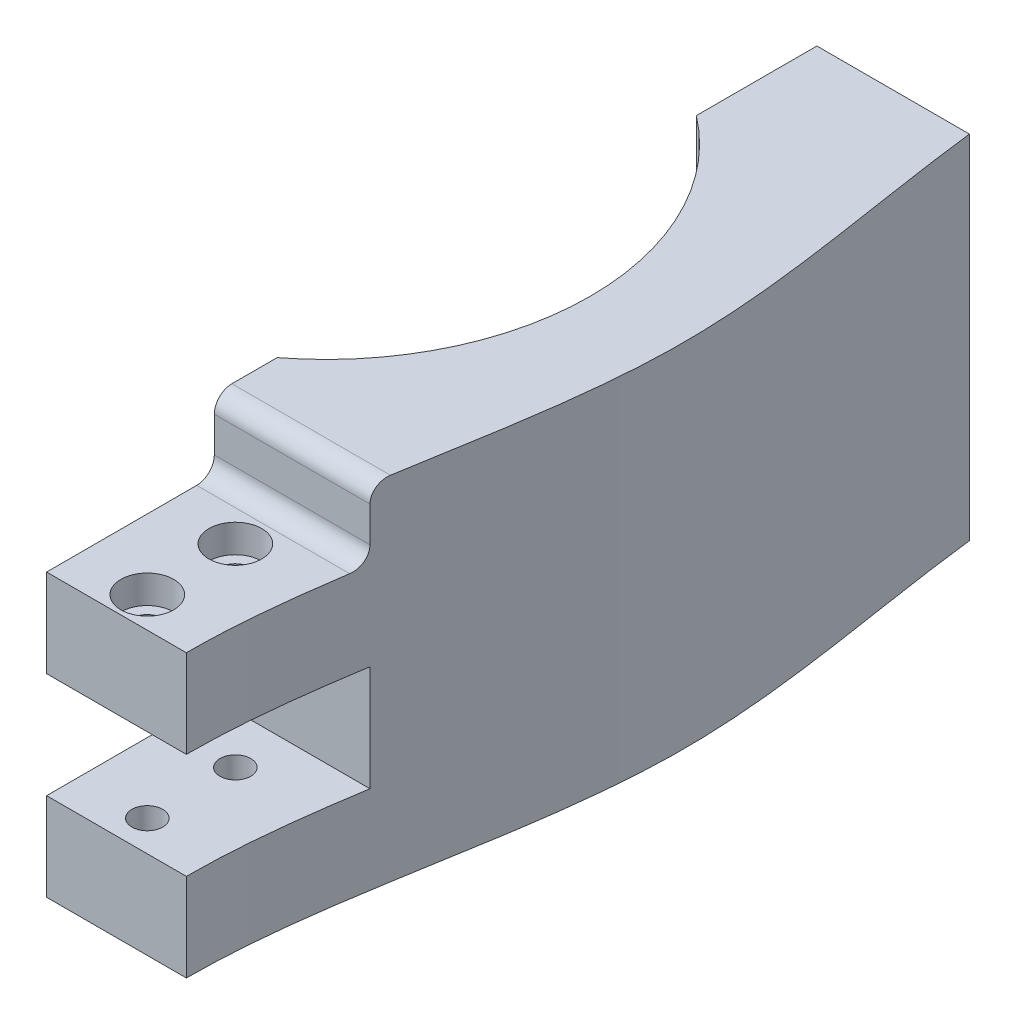
SolidWorks part; units mm, degrees
ref_plane "Front Plane" through (0, 0, 0) normal (0, 0, 1) x (1, 0, 0)
ref_plane "Top Plane" through (0, 0, 0) normal (0, 1, 0) x (1, 0, 0)
ref_plane "Right Plane" through (0, 0, 0) normal (1, 0, 0) x (0, 0, -1)
sketch "Sketch1" plane through (0, 0, 0) normal (0, 1, 0) x (1, 0, 0)
  line L0 (0, -50) -> (0, 50)
  line L1 (50, -50) -> (-50, -50)
  line L2 (50, -50) -> (50, 50)
  line L3 (50, 50) -> (-50, 50)
  line L4 (-50, -50) -> (-50, 50)
  line L5 (50, -50) -> (-50, 50) construction
  line L6 (50, 50) -> (-50, -50) construction
  circle A0 centre (0, 0) radius 30
  point P10 (0, 0)
  dimension "D1" = 60
  dimension "D2" = 100
extrude "Boss-Extrude1" add sketch "Sketch1" along normal blind 40 contours A0 L0 L3 L4 L1 | A0 L0 L1 L2 L3
sketch "Sketch2" plane through (0, 0, -50) normal (0, 0, -1) x (-1, 0, 0)
  line L0 (-50, 20) -> (50, 20) construction
  line L1 (0, 34.1421) -> (-14.1421, 20)
  line L2 (-14.1421, 20) -> (0, 5.8579)
  line L3 (0, 5.8579) -> (14.1421, 20)
  line L4 (14.1421, 20) -> (0, 34.1421)
  line L5 (-50, 40) -> (-50, 0) construction
  line L6 (50, 40) -> (50, 0) construction
  circle A0 centre (0, 20) radius 10 construction
  dimension "D1" = 20
extrude "Cut-Extrude1" [suppressed] cut sketch "Sketch2" against normal up to next
sketch "Sketch3" plane through (0, 0, 50) normal (0, 0, 1) x (1, 0, 0)
  line L0 (-50, 20) -> (50, 20) construction
  line L1 (-30.95, 40) -> (-18.25, 40)
  line L2 (-30.95, 40) -> (-30.95, 0)
  line L3 (-30.95, 0) -> (-18.25, 0)
  line L4 (-18.25, 40) -> (-18.25, 0)
  line L5 (-50, 40) -> (-50, 0) construction
  line L6 (50, 40) -> (50, 0) construction
  line L7 (-24.6, 40) -> (-24.6, 0) construction
  line L8 (50, 40) -> (-50, 40) construction
  point P10 (-30.95, 20)
  dimension "D1" = 12.7
  dimension "D2" = 25.4
extrude "Boss-Extrude2" add sketch "Sketch3" along normal blind 27.178
sketch "Sketch4" plane through (0, 0, 0) normal (1, 0, 0) x (0, 0, -1)
  line L1 (-92.4894, -65.8669) -> (92.4894, -65.8669)
  line L2 (-92.4894, -65.8669) -> (-92.4894, 65.8669)
  line L3 (-92.4894, 65.8669) -> (92.4894, 65.8669)
  line L4 (92.4894, -65.8669) -> (92.4894, 65.8669)
  line L5 (-92.4894, -65.8669) -> (92.4894, 65.8669) construction
  line L6 (-92.4894, 65.8669) -> (92.4894, -65.8669) construction
extrude "Cut-Extrude2" cut sketch "Sketch4" along normal through all
sketch "Sketch5" plane through (0, 0, 0) normal (1, 0, 0) x (0, 0, -1)
  line L1 (72.0832, -70.0065) -> (-72.0832, -70.0065)
  line L2 (72.0832, -70.0065) -> (72.0832, 70.0065)
  line L3 (72.0832, 70.0065) -> (-72.0832, 70.0065)
  line L4 (-72.0832, -70.0065) -> (-72.0832, 70.0065)
  line L5 (72.0832, -70.0065) -> (-72.0832, 70.0065) construction
  line L6 (72.0832, 70.0065) -> (-72.0832, -70.0065) construction
extrude "Cut-Extrude3" cut sketch "Sketch5" against normal up to surface (18.25 mm away) up to face at (-18.25, 20, 63.589)
sketch "Sketch6" plane through (0, 0, -50) normal (0, 0, -1) x (-1, 0, 0)
  line L0 (18.25, 40) -> (18.25, 0) construction
  line L2 (28.8566, 20) -> (18.25, 30.6066) construction
  line L3 (18.25, 30.6066) -> (7.6434, 20) construction
  line L4 (7.6434, 20) -> (18.25, 9.3934) construction
  line L5 (18.25, 9.3934) -> (28.8566, 20) construction
  circle A0 centre (18.25, 20) radius 7.5 construction
  circle A1 centre (18.25, 20) radius 20 construction
  circle A2 centre (5.5297, 22.15) radius 20
  dimension "D1" = 15
  dimension "D2" = 40
  dimension "D3" = 40
extrude "Cut-Extrude4" cut sketch "Sketch6" against normal blind 20
fillet "Fillet3" [suppressed] radius 6.35
fillet "Fillet4" radius 3.175 2 edges at (-18.25, 6.7164, -40) (-18.25, 37.5835, -40)
sketch "Sketch7" plane through (0, 0, 77.178) normal (0, 0, 1) x (1, 0, 0)
  line L1 (-48.3261, -46.7932) -> (48.3261, -46.7932)
  line L2 (-48.3261, -46.7932) -> (-48.3261, 46.7932)
  line L3 (-48.3261, 46.7932) -> (48.3261, 46.7932)
  line L4 (48.3261, -46.7932) -> (48.3261, 46.7932)
  line L5 (-48.3261, -46.7932) -> (48.3261, 46.7932) construction
  line L6 (-48.3261, 46.7932) -> (48.3261, -46.7932) construction
  point P0 (0, 0)
extrude "Cut-Extrude5" cut sketch "Sketch7" against normal up to surface (27.178 mm away) up to face at (-40.475, 20, 50)
sketch "Sketch8" plane through (0, 40, 0) normal (0, 1, 0) x (1, 0, 0)
  line L0 (-18.25, -50) -> (-50, -50) construction
  line L1 (-34.76, 50) -> (-50, 50)
  line L2 (-18.25, 50) -> (-50, 50) construction
  line L3 (-50, -50) -> (-50, 50) construction
  line L4 (-50, -50) -> (-50, 50)
  line L5 (-34.125, -50) -> (-50, -50)
  spline S0 degree 3 poles (-34.125, -50) (-34.125, -33.2412) (-45.237, -0.0937) (-34.76, 33.3302) (-34.76, 50) knots 0 0 0 0 0.50037 1 1 1 1
  point P16 (-50, 0)
  dimension "D1" = 10.16
  dimension "D2" = 15.24
extrude "Cut-Extrude6" cut sketch "Sketch8" against normal through all
sketch "Sketch9" plane through (0, 40, 0) normal (0, 1, 0) x (1, 0, 0)
  line L0 (-18.25, -30.95) -> (-35.933, -30.95)
  line L1 (-18.25, -50) -> (-18.25, -23.8104) construction
  line L2 (-18.25, -30.95) -> (-18.25, -50)
  line L3 (-18.25, -50) -> (-34.125, -50)
  spline S0 degree 3 poles (-2004.9014, -357.9043) (168.4568, -203.1879) (-248.5847, -1.5) (169.3358, 210.8777) (-2014.0992, 296.1428) knots -2.59149 -2.59149 -2.59149 -2.59149 0.50037 3.62745 3.62745 3.62745 3.62745 only from (-34.125, -50) to (-34.76, 50) construction
  spline S1 degree 3 poles (-34.125, -50) (-34.125, -33.2412) (-45.237, -0.0937) (-34.76, 33.3302) (-34.76, 50) knots 0 0 0 0 0.50037 1 1 1 1
  spline M3 degree 3 poles (-34.76, 50) (-34.76, 33.3302) (-45.237, -0.0937) (-34.125, -33.2412) (-34.125, -50) knots 0 0 0 0 0.49963 1 1 1 1
  line M4 (-34.125, -50) -> (-18.25, -50)
  line M5 (-18.25, -50) -> (-18.25, -23.8104)
  dimension "D1" = 19.05
extrude "Cut-Extrude7" cut sketch "Sketch9" against normal blind 8 contours L0 M5 M3 M4
ref_plane "Plane1" through (0, 16, 0) normal (0, 1, 0) x (1, 0, 0)
mirror "Mirror1" [suppressed] about plane through (0, 16, 0) normal (0, 1, 0)
fillet "Fillet5" radius 2 2 edges at (-27.0915, 32, 30.95) (-27.0915, 40, 30.95)
sketch "Sketch10" plane through (0, 32, 0) normal (0, 1, 0) x (1, 0, 0)
  line L0 (-26.1875, -50) -> (-26.1875, -32.95) construction
  line L1 (-34.125, -50) -> (-18.25, -50) construction
  line L2 (-18.25, -32.95) -> (-35.6232, -32.95) construction
  circle A0 centre (-26.1875, -46.5) radius 1.75
  circle A1 centre (-26.1875, -36.5) radius 1.75
  dimension "D1" = 3.5
  dimension "D4" = 3.5
  dimension "D2" = 10
  dimension "D3" = 3.5
extrude "Cut-Extrude8" cut sketch "Sketch10" against normal through all
sketch "Sketch11" plane through (0, 0, 50) normal (0, 0, 1) x (1, 0, 0)
  line L0 (-34.125, 16) -> (-18.25, 16) construction
  line L2 (-34.125, 10) -> (-18.25, 10)
  line L3 (-34.125, 10) -> (-34.125, 22)
  line L4 (-34.125, 32) -> (-34.125, 0)
  line L5 (-34.125, 0) -> (-18.25, 0)
  line L6 (-18.25, 0) -> (-18.25, 32)
  line L7 (-18.25, 32) -> (-34.125, 32)
  line L8 (-34.125, 32) -> (-34.125, 0) construction
  line L10 (-18.25, 0) -> (-18.25, 32) construction
  line L11 (-18.25, 32) -> (-34.125, 32) construction
  line L12 (-34.125, 22) -> (-18.25, 22)
  line L13 (-18.25, 10) -> (-18.25, 22)
  line L14 (-34.125, 10) -> (-18.25, 22) construction
  line L15 (-34.125, 22) -> (-18.25, 10) construction
  line L16 (-26.1875, 22) -> (-43.6768, 22)
  line L17 (-26.1875, 22) -> (-26.1875, 10)
  line L18 (-26.1875, 10) -> (-43.6768, 10)
  line L19 (-43.6768, 22) -> (-43.6768, 10)
  line L23 (-34.125, 0) -> (-18.25, 0)
  point P6 (-26.1875, 16)
  line M9 (-34.125, 32) -> (-34.125, 0)
  line M11 (-18.25, 0) -> (-18.25, 32)
  dimension "D2" = 12
  dimension "D1" = 0
extrude "Cut-Extrude9" cut sketch "Sketch11" against normal blind 19.05 contours L16 L19 L18 M9 | L17 L12 L2 M9 | L12 L17 L2 M11
sketch "Sketch14" plane through (0, 32, 0) normal (0, 1, 0) x (1, 0, 0)
  circle A0 centre (-26.1875, -36.5) radius 3
  circle A1 centre (-26.1875, -46.5) radius 3
  dimension "D1" = 6
  dimension "D2" = 6
extrude "Cut-Extrude10" cut sketch "Sketch14" against normal blind 3.2
mirror "Mirror2" about plane through (0, 16, 0) normal (0, 1, 0) of "Cut-Extrude10"
sketch "Sketch15" plane through (0, 0, -50) normal (0, 0, -1) x (-1, 0, 0)
  line L1 (0, 0) -> (61.0985, 0)
  line L2 (0, 0) -> (0, 49.7438)
  line L3 (0, 49.7438) -> (61.0985, 49.7438)
  line L4 (61.0985, 0) -> (61.0985, 49.7438)
extrude "Cut-Extrude11" cut sketch "Sketch15" against normal blind 12.5
mirror "Mirror3" about plane through (0, 0, 0) normal (1, 0, 0) of bodies 115
delete or keep bodies "Body-Delete/Keep 1" type delete bodies bodies 115
